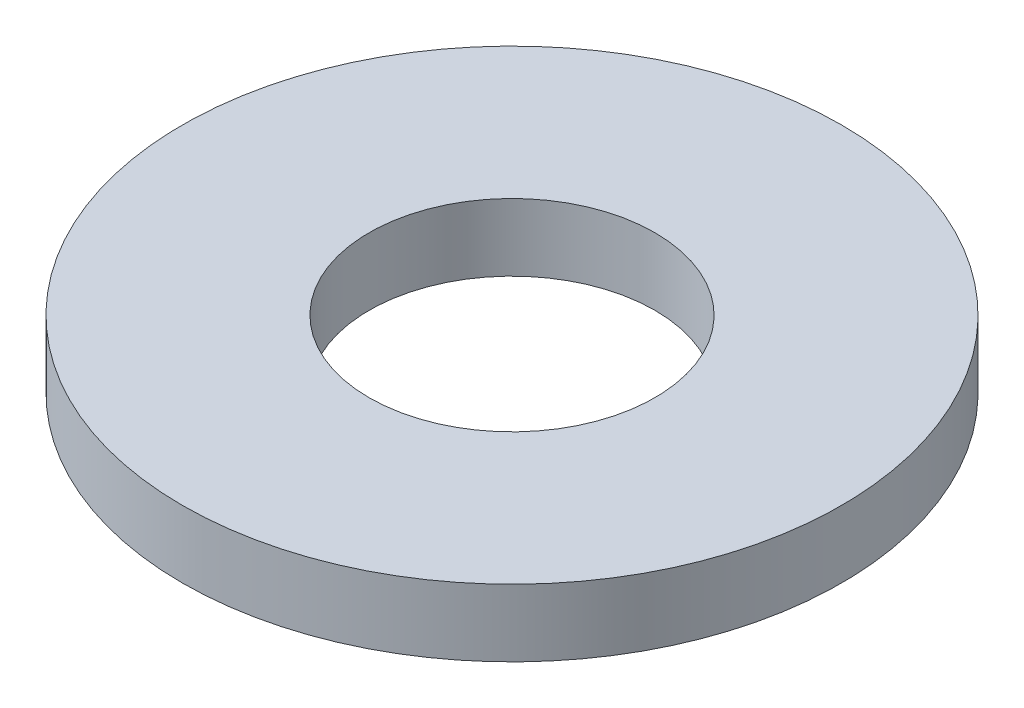
SolidWorks part; units mm, degrees
material "2.0402 (CuZn40Pb2)"
ref_plane "Front Plane" through (0, 0, 0) normal (0, 0, 1) x (1, 0, 0)
ref_plane "Top Plane" through (0, 0, 0) normal (0, 1, 0) x (1, 0, 0)
ref_plane "Right Plane" through (0, 0, 0) normal (1, 0, 0) x (0, 0, -1)
sketch "Sketch1" plane through (0, 0, 0) normal (0, 1, 0) x (1, 0, 0)
  circle A0 centre (0, 0) radius 9.8
  circle A1 centre (0, 0) radius 4.25
extrude "Boss-Extrude1" add sketch "Sketch1" along normal blind 2
